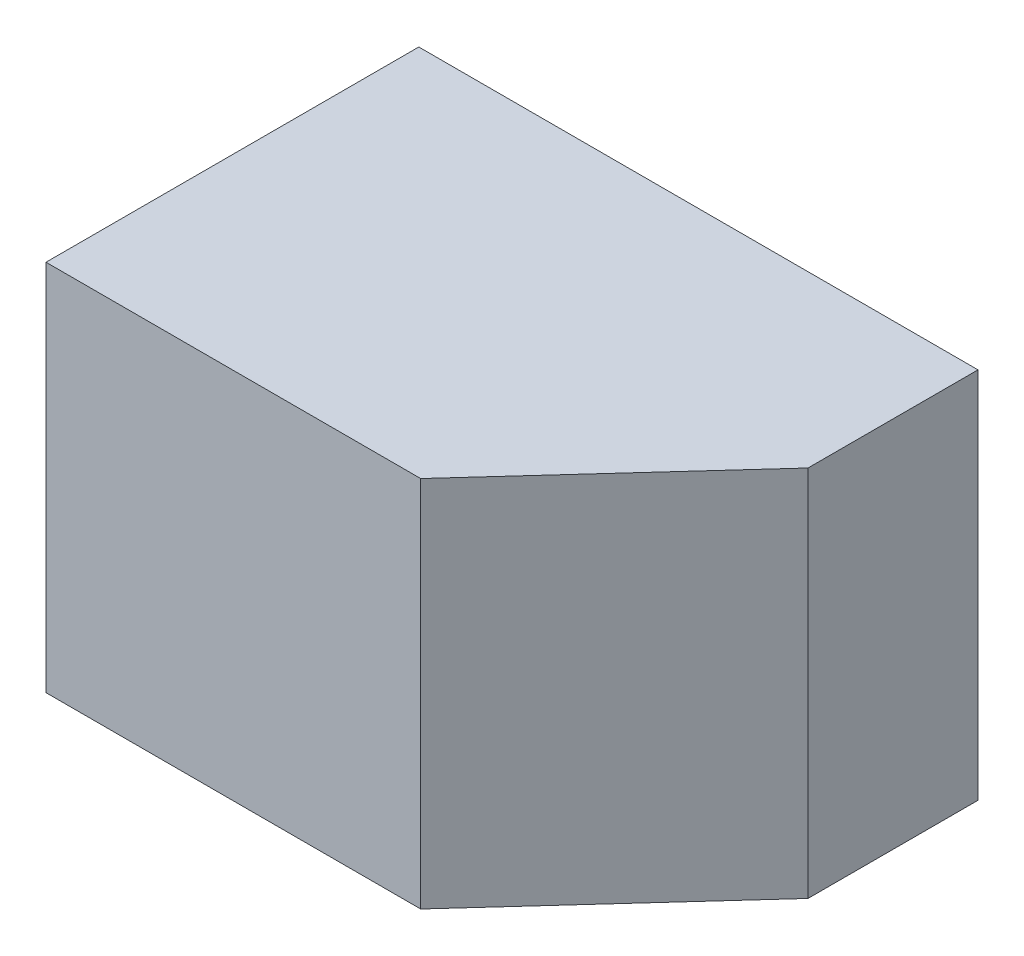
SolidWorks part; units mm, degrees
ref_plane "Спереди" through (0, 0, 0) normal (0, 0, 1) x (1, 0, 0)
ref_plane "Сверху" through (0, 0, 0) normal (0, 1, 0) x (1, 0, 0)
ref_plane "Справа" through (0, 0, 0) normal (1, 0, 0) x (0, 0, -1)
sketch "Эскиз1" plane through (0, 0, 0) normal (1, 0, 0) x (0, 0, -1)
  line L1 (0, 0) -> (10, 0)
  line L2 (0, 0) -> (0, 10)
  line L3 (0, 10) -> (10, 10)
  line L4 (10, 0) -> (10, 10)
  dimension "D1" = 10
  dimension "D2" = 10
extrude "Бобышка-Вытянуть1" add sketch "Эскиз1" along normal blind 15
sketch "Эскиз2" plane through (0, 10, 0) normal (0, 1, 0) x (1, 0, 0)
  line L0 (10.0505, 0) -> (15, 5.4401)
  line L1 (15, 0) -> (0, 0) construction
  line L2 (15, 10) -> (15, 0) construction
  line L3 (15, 5.4401) -> (15, 0)
  line L4 (15, 0) -> (10.0505, 0)
extrude "Вырез-Вытянуть1" cut sketch "Эскиз2" against normal blind 15
